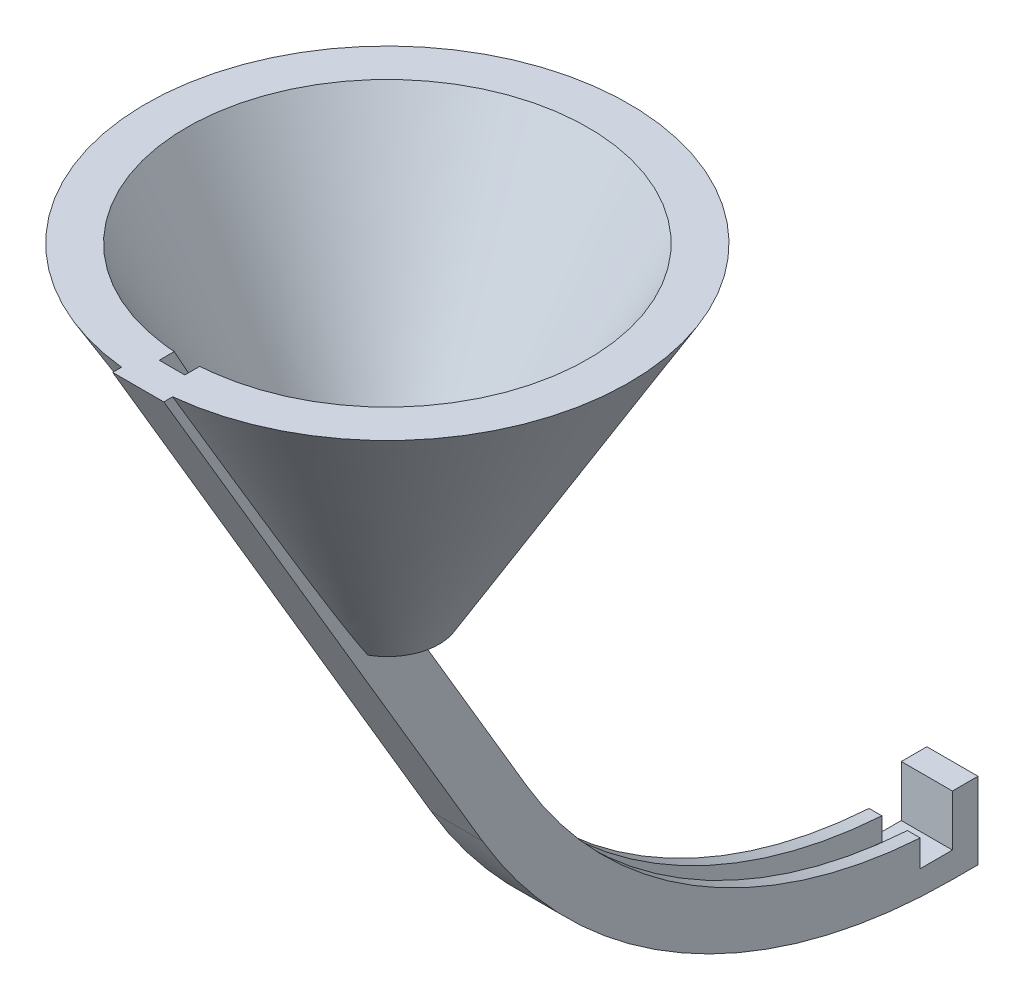
SolidWorks part; units mm, degrees
ref_plane "Front Plane" through (0, 0, 0) normal (0, 0, 1) x (1, 0, 0)
ref_plane "Top Plane" through (0, 0, 0) normal (0, 1, 0) x (1, 0, 0)
ref_plane "Right Plane" through (0, 0, 0) normal (1, 0, 0) x (0, 0, -1)
sketch "Sketch1" plane through (0, 0, 0) normal (0, 1, 0) x (1, 0, 0)
  circle A0 centre (0, 0) radius 30
  dimension "D1" = 60
sketch "Sketch3" plane through (0, 0, 0) normal (1, 0, 0) x (0, 0, -1)
  line L0 (0, 16.1146) -> (0, -58.8622) construction
  point P2 (0, -75.1347)
  point P3 (0, 36.7171)
  point P4 (0, 16.1146)
  point P5 (0, -58.8622)
sketch "Sketch2" plane through (0, 0, 0) normal (1, 0, 0) x (0, 0, -1)
  line L1 (30, 0) -> (-30, 0) construction
  line L2 (0, -50.8) -> (-30, 0)
  line L4 (0, 0) -> (0, -50.8)
  line L5 (-30, 0) -> (0, 0)
  dimension "D1" = 30
revolve "Revolve1" add sketch "Sketch2" angle 360 about L4
sketch "Sketch4" plane through (0, 0, 0) normal (1, 0, 0) x (0, 0, -1)
  line L0 (0, -45.72) -> (-24.92, 0)
  line L1 (0, 16.1146) -> (0, -58.8622) construction
  line L2 (30, 0) -> (-30, 0) construction
  line L3 (-24.92, 0) -> (0, 0)
  line L4 (0, 0) -> (0, -45.72)
  dimension "D1" = 5.08
  dimension "D2" = 5.08
revolve "Cut-Revolve1" cut sketch "Sketch4" angle 360 about L0
sketch "Sketch5" plane through (0, 0, 0) normal (1, 0, 0) x (0, 0, -1)
  line L0 (0, 16.1146) -> (0, -58.8622) construction
  line L1 (6.44, -39.8949) -> (-6.44, -39.8949)
  line L2 (6.44, -39.8949) -> (6.44, -55.7296)
  line L3 (6.44, -55.7296) -> (-6.44, -55.7296)
  line L4 (-6.44, -39.8949) -> (-6.44, -55.7296)
  line L5 (0, -50.8) -> (30, 0) construction
  line L6 (-24.92, 0) -> (0, -45.72) construction
  line L7 (30, 0) -> (-30, 0) construction
  line L8 (0, -45.72) -> (24.92, 0) construction
  point P4 (0, -39.8949)
  point P7 (3.175, -39.8949)
  point P18 (-3.175, -39.8949)
  dimension "D1" = 6.35
  dimension "D2" = 5.08
  dimension "D3" = 5.08
extrude "Cut-Extrude2" cut sketch "Sketch5" against normal mid plane 15.24
sketch "Sketch6" plane through (0, 0, 0) normal (1, 0, 0) x (0, 0, -1)
  line L0 (-7.3746, -39.8949) -> (8.6493, -67.0288)
  line L1 (66.99, -93.98) -> (66.99, -90.805)
  line L2 (66.99, -90.805) -> (70.165, -90.805)
  line L3 (70.165, -90.805) -> (70.165, -100.33)
  line L5 (0, -39.8949) -> (14.1171, -63.7998)
  line L6 (-30, 0) -> (-6.44, -39.8949) construction
  line L7 (30, 0) -> (-30, 0) construction
  line L8 (0, 16.1146) -> (0, -58.8622) construction
  line L11 (0, -39.8949) -> (-23.56, 0)
  line L12 (0, -39.8949) -> (-7.3746, -39.8949)
  line L13 (-23.56, 0) -> (-30.9346, 0)
  line L14 (-7.3746, -39.8949) -> (-30.9346, 0)
  line L15 (-6.44, -39.8949) -> (6.44, -39.8949) construction
  line L16 (66.99, -100.33) -> (70.165, -100.33)
  arc A0 (8.6493, -67.0288) -> (46.99, -97.3109) centre (66.99, -32.5756) ccw
  arc A1 (14.1171, -63.7998) -> (66.99, -93.98) centre (66.99, -32.5756) ccw
  arc A2 (46.99, -97.3109) -> (66.99, -100.33) centre (66.99, -32.5756) ccw
  point P6 (57.1172, -100.33)
  point P7 (78.5965, -100.33)
  point P12 (58.2088, -100.33)
  dimension "D1" = 3.175
  dimension "D3" = 3.175
  dimension "D2" = 6.35
  dimension "D4" = 6.35
  dimension "D5" = 100.33
  dimension "D6" = 46.99
  dimension "D7" = 20
extrude "Boss-Extrude1" add sketch "Sketch6" along normal mid plane 6.35
sketch "Sketch7" plane through (0, 0, 0) normal (1, 0, 0) x (0, 0, -1)
  line L0 (-3.175, -39.8949) -> (11.763, -65.19)
  line L1 (14.1171, -63.7998) -> (0, -39.8949) construction
  line L2 (0, 16.1146) -> (0, -58.8622) construction
  line L3 (-3.175, -39.8949) -> (-26.735, 0)
  line L4 (30, 0) -> (-30, 0) construction
  line L5 (-5.603, -39.8949) -> (0, -39.8949) construction
  line L8 (-23.56, 0) -> (-26.735, 0)
  line L9 (14.1171, -63.7998) -> (-23.56, 0)
  line L10 (66.99, -97.155) -> (66.99, -93.98)
  arc A0 (11.763, -65.19) -> (59.1577, -96.2339) centre (66.99, -32.5756) ccw
  arc A1 (14.1171, -63.7998) -> (66.99, -93.98) centre (66.99, -32.5756) ccw construction
  arc A4 (14.1171, -63.7998) -> (50.5049, -91.7258) centre (66.99, -32.5756) ccw
  arc A7 (59.1577, -96.2339) -> (66.99, -97.155) centre (149.1668, 635.3314) ccw
  arc A8 (14.1171, -63.7998) -> (66.99, -93.98) centre (66.99, -32.5756) ccw construction
  arc A9 (66.99, -93.98) -> (50.5049, -91.7258) centre (66.99, -32.5756) cw
  dimension "D1" = 3.175
  dimension "D2" = 3.175
extrude "Cut-Extrude4" cut sketch "Sketch7" against normal blind 1.5875 contours L0 A0 A7 L10 A9 A4 L9 L8 L3
mirror "Mirror1" about plane through (0, 0, 0) normal (1, 0, 0) of "Cut-Extrude4"
sketch "Sketch9" plane through (0, 0, 0) normal (1, 0, 0) x (0, 0, -1)
  line L0 (0, 0) -> (-24.92, 0)
  line L1 (-24.92, 0) -> (-2.8015, -39.8949)
  line L2 (-5.603, -39.8949) -> (0, -39.8949) construction
  line L3 (-2.8015, -39.8949) -> (0, -39.8949)
  line L4 (0, -39.8949) -> (0, 0)
  dimension "D1" = 24.92
revolve "Cut-Revolve2" cut sketch "Sketch9" angle 360 about L0
sketch "Sketch10" plane through (-3.175, 0, 0) normal (-1, 0, 0) x (0, 0, 1)
  line L0 (-66.99, -93.98) -> (-66.99, -90.805) construction
  line L1 (-66.99, -93.8496) -> (-62.99, -93.8496)
  line L2 (-66.99, -93.8496) -> (-66.99, -97.155)
  line L3 (-66.99, -97.155) -> (-62.99, -97.155)
  line L4 (-62.99, -93.8496) -> (-62.99, -97.155)
  arc A0 (-66.99, -93.98) -> (-14.1171, -63.7998) centre (-66.99, -32.5756) ccw construction
  point P4 (-66.99, -92.856)
  point P8 (-62.99, -93.8496)
  dimension "D2" = 4
extrude "Cut-Extrude5" cut sketch "Sketch10" against normal through all
